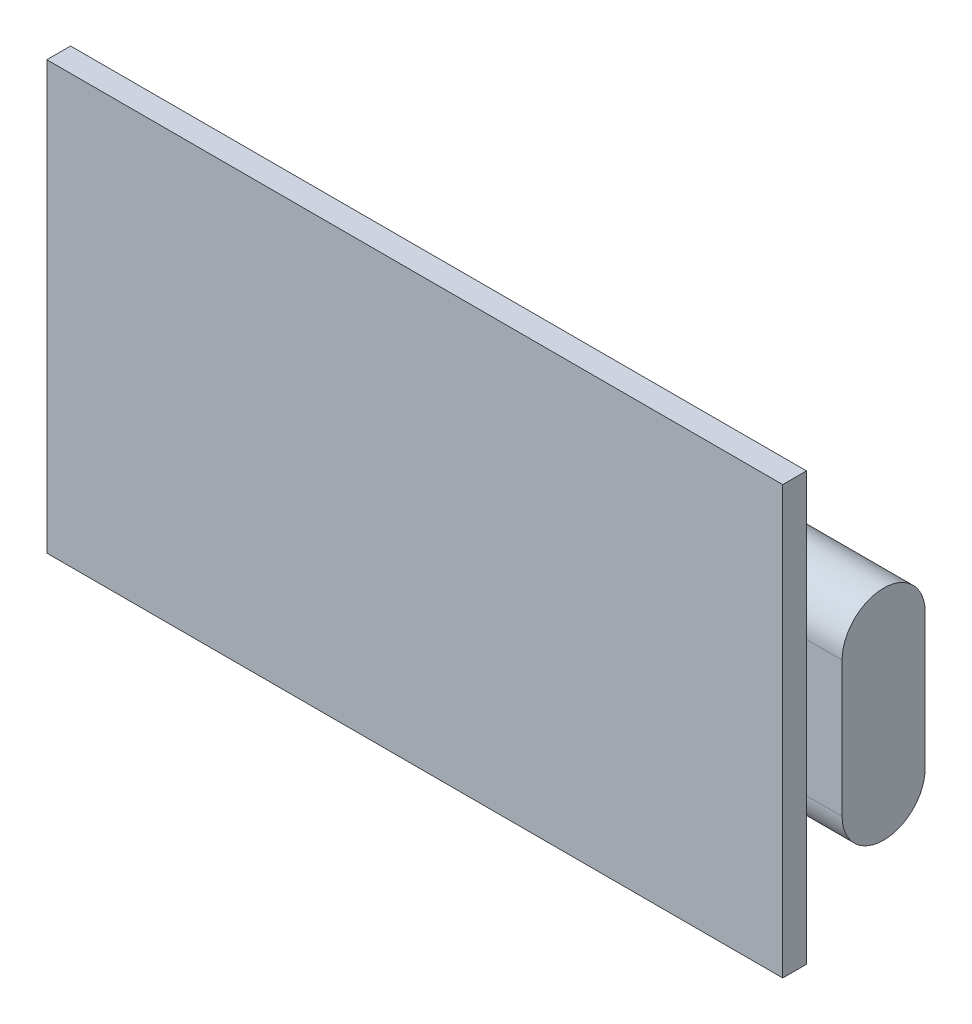
SolidWorks part; units mm, degrees
ref_plane "Plano frontal" through (0, 0, 0) normal (0, 0, 1) x (1, 0, 0)
ref_plane "Plano superior" through (0, 0, 0) normal (0, 1, 0) x (1, 0, 0)
ref_plane "Plano direito" through (0, 0, 0) normal (1, 0, 0) x (0, 0, -1)
sketch "Esboço1" plane through (0, 0, 0) normal (0, 0, 1) x (1, 0, 0)
  line L1 (-15.5, 9) -> (15.5, 9)
  line L2 (-15.5, 9) -> (-15.5, -9)
  line L3 (-15.5, -9) -> (15.5, -9)
  line L4 (15.5, 9) -> (15.5, -9)
  line L5 (-15.5, 9) -> (15.5, -9) construction
  line L6 (-15.5, -9) -> (15.5, 9) construction
  point P0 (0, 0)
  dimension "D1" = 31
  dimension "D2" = 18
extrude "Ressalto-extrusão1" add sketch "Esboço1" along normal blind 1
sketch "Esboço2" plane through (15.5, 0, 0) normal (1, 0, 0) x (0, 0, -1)
  line L0 (1.75, 2.85) -> (1.75, -2.85) construction
  line L1 (3.5, 2.85) -> (3.5, -2.85)
  line L2 (0, 2.85) -> (0, -2.85)
  line L3 (0, -9) -> (0, 9) construction
  arc A0 (3.5, 2.85) -> (0, 2.85) centre (1.75, 2.85) ccw
  arc A1 (0, -2.85) -> (3.5, -2.85) centre (1.75, -2.85) ccw
  point P2 (1.75, 0)
  point P7 (2.8913, -0.4753)
  point P8 (0, -3.193)
  point P11 (0, 0)
  point P12 (1.75, 3.7157)
  dimension "D1" = 1.75
  dimension "D2" = 9.2
extrude "Ressalto-extrusão2" add sketch "Esboço2" along normal blind 1.5 and the other way blind 6
